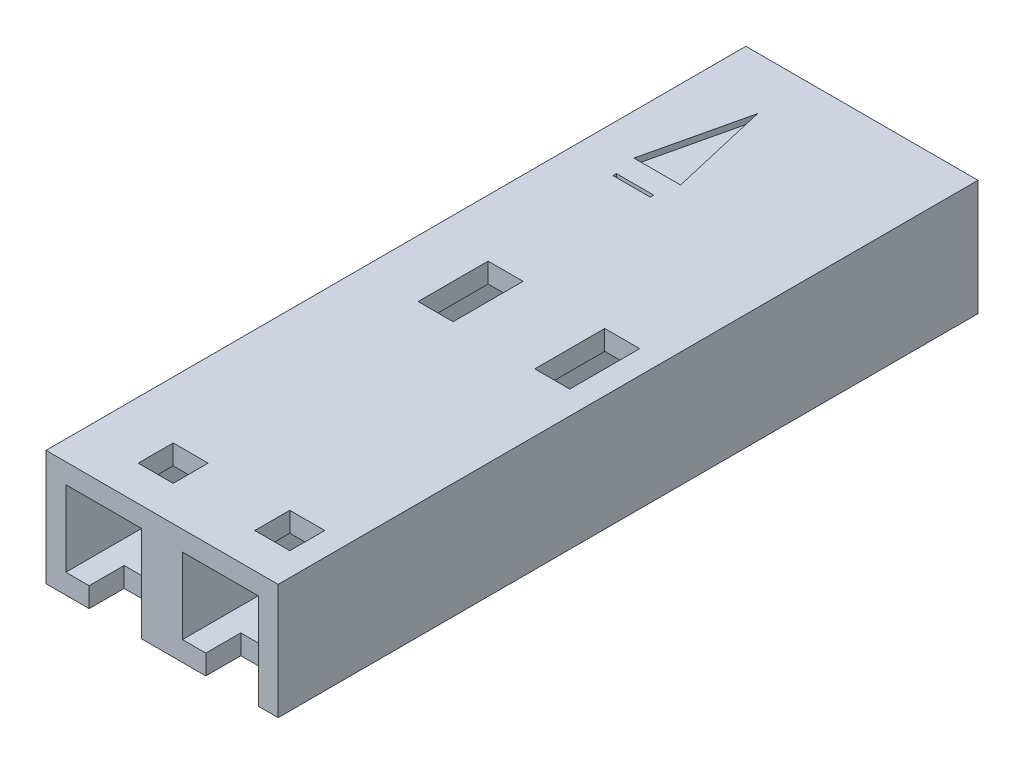
SolidWorks part; units mm, degrees
ref_plane "Front" through (0, 0, 0) normal (0, 0, 1) x (1, 0, 0)
ref_plane "Top" through (0, 0, 0) normal (0, 1, 0) x (1, 0, 0)
ref_plane "Right" through (0, 0, 0) normal (1, 0, 0) x (0, 0, -1)
sketch "Sketch1" plane through (0, 0, 0) normal (0, 0, 1) x (1, 0, 0)
  line L0 (0, 0) -> (5.0546, 0)
  line L1 (5.0546, 0) -> (5.0546, 2.5146)
  line L2 (5.0546, 2.5146) -> (0, 2.5146)
  line L3 (0, 2.5146) -> (0, 0)
  dimension "D1" = 5.0546
  dimension "D2" = 2.5146
extrude "Boss-Extrude1" add sketch "Sketch1" along normal blind 15.24
sketch "Sketch2" plane through (0, 0, 0) normal (0, 0, -1) x (-1, 0, 0)
  line L0 (-4.3688, 1.8288) -> (-3.2258, 1.8288)
  line L1 (-3.2258, 1.8288) -> (-3.2258, 0.6858)
  line L2 (-3.2258, 0.6858) -> (-4.3688, 0.6858)
  line L3 (-4.3688, 0.6858) -> (-4.3688, 1.8288)
  line L4 (-1.8288, 1.8288) -> (-0.6858, 1.8288)
  line L5 (-0.6858, 1.8288) -> (-0.6858, 0.6858)
  line L6 (-0.6858, 0.6858) -> (-1.8288, 0.6858)
  line L7 (-1.8288, 0.6858) -> (-1.8288, 1.8288)
  line L8 (-3.7973, 1.8288) -> (-3.7973, 0.6858) construction
  line L9 (-1.2573, 1.8288) -> (-1.2573, 0.6858) construction
  line L10 (-3.2258, 1.2573) -> (-4.3688, 1.2573) construction
  line L11 (-0.6858, 1.2573) -> (-1.8288, 1.2573) construction
  line L12 (-2.5273, 2.5146) -> (-2.5273, 0) construction
  line L13 (-5.0546, 2.5146) -> (0, 2.5146) construction
  line L14 (0, 0) -> (-5.0546, 0) construction
  dimension "D1" = 2.54
  dimension "D2" = 1.143
  dimension "D3" = 1.143
  dimension "D4" = 1.143
  dimension "D5" = 1.143
  dimension "D6" = 1.2573
  dimension "D7" = 1.2573
extrude "Cut-Extrude1" cut sketch "Sketch2" against normal through all
chamfer "Chamfer1" distance 0.254 angle 45 8 edges at (0.6858, 1.2573, 0) (1.2573, 0.6858, 0) (1.8288, 1.2573, 0) (1.2573, 1.8288, 0) (4.3688, 1.2573, 0) (3.7973, 0.6858, 0) (3.2258, 1.2573, 0) (3.7973, 1.8288, 0)
sketch "Sketch3" plane through (0, 2.5146, 0) normal (0, 1, 0) x (1, 0, 0)
  line L0 (3.7846, -13.716) -> (4.5466, -13.716)
  line L1 (4.5466, -13.716) -> (4.5466, -14.478)
  line L2 (4.5466, -14.478) -> (3.7846, -14.478)
  line L3 (3.7846, -14.478) -> (3.7846, -13.716)
  line L4 (1.2446, -13.716) -> (2.0066, -13.716)
  line L5 (2.0066, -13.716) -> (2.0066, -14.478)
  line L6 (2.0066, -14.478) -> (1.2446, -14.478)
  line L7 (1.2446, -14.478) -> (1.2446, -13.716)
  line L8 (1.6256, -13.716) -> (1.6256, -14.478) construction
  line L9 (4.1656, -13.716) -> (4.1656, -14.478) construction
  line L10 (1.2446, -14.097) -> (2.0066, -14.097) construction
  line L11 (3.7846, -14.097) -> (4.5466, -14.097) construction
  line L12 (5.0546, -15.24) -> (0, -15.24) construction
  line L13 (5.0546, -15.24) -> (5.0546, 0) construction
  line L14 (3.7846, -8.382) -> (3.7846, -6.858)
  line L15 (3.7846, -6.858) -> (4.5466, -6.858)
  line L16 (4.5466, -6.858) -> (4.5466, -8.382)
  line L17 (4.5466, -8.382) -> (3.7846, -8.382)
  line L18 (1.2446, -6.858) -> (2.0066, -6.858)
  line L19 (2.0066, -6.858) -> (2.0066, -8.382)
  line L20 (2.0066, -8.382) -> (1.2446, -8.382)
  line L21 (1.2446, -8.382) -> (1.2446, -6.858)
  line L22 (0, -7.62) -> (5.0546, -7.62) construction
  line L23 (0, -15.24) -> (0, 0) construction
  line L24 (1.2446, -7.62) -> (2.0066, -7.62) construction
  line L25 (3.7846, -7.62) -> (4.5466, -7.62) construction
  dimension "D1" = 0.381
  dimension "D2" = 0.381
  dimension "D3" = 0.381
  dimension "D4" = 0.381
  dimension "D5" = 2.54
  dimension "D6" = 0.762
  dimension "D7" = 0.508
  dimension "D8" = 1.524
extrude "Cut-Extrude2" cut sketch "Sketch3" against normal blind 1.27
ref_plane "Plane1" through (0, 0, 0.508) normal (0, 0, 1) x (1, 0, 0)
sketch "Sketch4" plane through (0, 0, 0.508) normal (0, 0, 1) x (1, 0, 0)
  line L0 (2.0828, 2.0828) -> (0.4318, 2.0828) construction
  line L1 (0.4318, 2.0828) -> (0.4318, 0.4318) construction
  line L2 (0.4318, 0.4318) -> (2.0828, 0.4318) construction
  line L3 (2.0828, 0.4318) -> (2.0828, 2.0828) construction
  line L4 (2.9718, 2.0828) -> (2.9718, 0.4318) construction
  line L5 (4.6228, 2.0828) -> (2.9718, 2.0828) construction
  line L6 (4.6228, 0.4318) -> (4.6228, 2.0828) construction
  line L7 (2.9718, 0.4318) -> (4.6228, 0.4318) construction
  line L8 (2.0828, 2.0828) -> (0.4318, 2.0828)
  line L9 (0.4318, 2.0828) -> (0.4318, 0.4318)
  line L10 (0.4318, 0.4318) -> (2.0828, 0.4318)
  line L11 (2.0828, 0.4318) -> (2.0828, 2.0828)
  line L12 (2.9718, 2.0828) -> (2.9718, 0.4318)
  line L13 (4.6228, 2.0828) -> (2.9718, 2.0828)
  line L14 (4.6228, 0.4318) -> (4.6228, 2.0828)
  line L15 (2.9718, 0.4318) -> (4.6228, 0.4318)
extrude "Cut-Extrude3" cut sketch "Sketch4" along normal through all
sketch "Sketch6" plane through (0, 0, 0) normal (0, -1, 0) x (1, 0, 0)
  line L0 (0.9398, 15.24) -> (2.0828, 15.24)
  line L1 (0, 15.24) -> (5.0546, 15.24) construction
  line L2 (2.0828, 15.24) -> (2.0828, 14.478)
  line L3 (2.0828, 15.24) -> (2.0828, 0.508) construction
  line L4 (2.0828, 14.478) -> (0.9398, 14.478)
  line L5 (0.9398, 14.478) -> (0.9398, 15.24)
  line L6 (4.6228, 15.24) -> (4.6228, 14.478)
  line L7 (4.6228, 15.24) -> (4.6228, 0.508) construction
  line L8 (4.6228, 14.478) -> (3.4798, 14.478)
  line L9 (3.4798, 14.478) -> (3.4798, 15.24)
  line L10 (3.4798, 15.24) -> (4.6228, 15.24)
  line L11 (1.2446, 14.478) -> (2.0066, 14.478) construction
  dimension "D1" = 1.143
  dimension "D2" = 1.143
extrude "Cut-Extrude5" cut sketch "Sketch6" against normal up to surface (0.4318 mm away) up to face at (1.2573, 0.4318, 7.874)
sketch "Sketch7" plane through (0, 0, 0) normal (0, -1, 0) x (1, 0, 0)
  line L0 (2.2098, 7.62) -> (2.7178, 7.62)
  line L1 (2.7178, 7.62) -> (2.7178, 0)
  line L2 (0, 0) -> (5.0546, 0) construction
  line L3 (2.7178, 0) -> (2.2098, 0)
  line L4 (2.2098, 0) -> (2.2098, 7.62)
  line L5 (5.0546, 7.62) -> (0, 7.62) construction
  line L6 (5.0546, 15.24) -> (5.0546, 0) construction
  line L7 (0, 15.24) -> (0, 0) construction
  line L8 (2.0828, 14.478) -> (2.0828, 0.508) construction
  dimension "D1" = 0.127
  dimension "D2" = 0.508
extrude "Cut-Extrude6" cut sketch "Sketch7" against normal blind 0.762
sketch "Sketch8" plane through (0, 2.5146, 0) normal (0, 1, 0) x (1, 0, 0)
  line L0 (1.397, -1.143) -> (0.889, -3.3274)
  line L1 (0.889, -3.3274) -> (1.905, -3.3274)
  line L2 (1.905, -3.3274) -> (1.397, -1.143)
  line L3 (1.397, 1.3415) -> (1.397, -3.8862) construction
  line L4 (0.9906, -3.81) -> (1.8034, -3.81)
  line L5 (1.8034, -3.81) -> (1.8034, -3.8862)
  line L6 (1.8034, -3.8862) -> (0.9906, -3.8862)
  line L7 (0.9906, -3.81) -> (0.9906, -3.8862)
  line L8 (5.0546, 0) -> (0, 0) construction
  dimension "D1" = 2.1844
  dimension "D2" = 1.016
  dimension "D3" = 0.8128
  dimension "D4" = 0.0762
  dimension "D5" = 1.143
  dimension "D6" = 2.667
  dimension "D7" = 1.397
extrude "Cut-Extrude7" cut sketch "Sketch8" against normal blind 0.127
sketch "Sketch10" plane through (0, 0, 0.508) normal (0, 0, 1) x (1, 0, 0)
  line L0 (0.6858, 0.6858) -> (1.8288, 1.8288) construction
  line L1 (3.2258, 0.6858) -> (4.3688, 1.8288) construction
  point P4 (1.2573, 1.2573)
  point P9 (3.7973, 1.2573)
